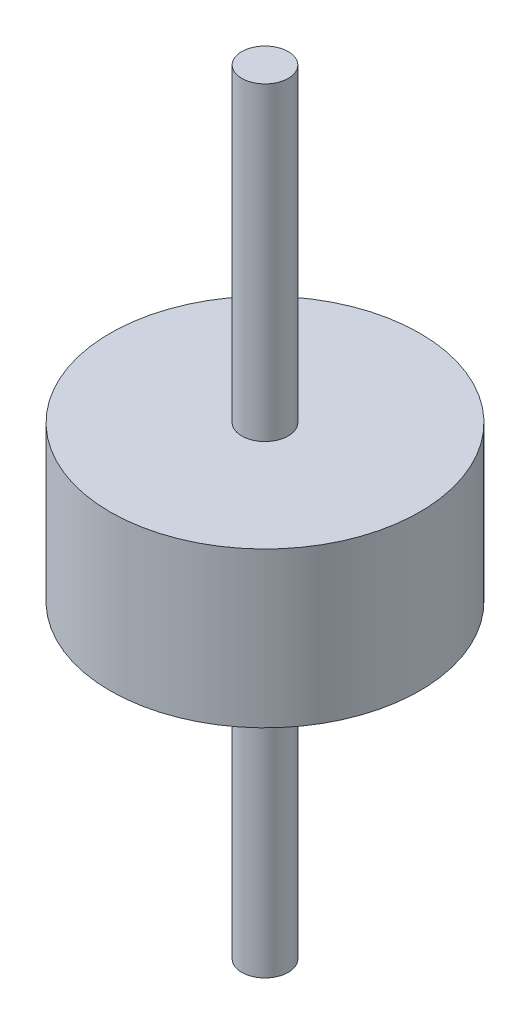
SolidWorks part; units mm, degrees
ref_plane "Front Plane" through (0, 0, 0) normal (0, 0, 1) x (1, 0, 0)
ref_plane "Top Plane" through (0, 0, 0) normal (0, 1, 0) x (1, 0, 0)
ref_plane "Right Plane" through (0, 0, 0) normal (1, 0, 0) x (0, 0, -1)
sketch "Sketch1" plane through (0, 0, 0) normal (0, 1, 0) x (1, 0, 0)
  circle A0 centre (-10.1199, -11.3021) radius 5.08
  dimension "D1" = 10.16
extrude "Boss-Extrude2" add sketch "Sketch1" along normal blind 5.08
sketch "Sketch2" plane through (0, 5.08, 0) normal (0, 1, 0) x (1, 0, 0)
  circle A0 centre (-10.1199, -11.3021) radius 0.762
  dimension "D1" = 1.524
extrude "Boss-Extrude3" add sketch "Sketch2" along normal blind 10.16 contours A0
sketch "Sketch3" plane through (0, 0, 0) normal (0, -1, 0) x (1, 0, 0)
  circle A1 centre (-10.1199, 11.3021) radius 0.762
  dimension "D1" = 1.524
extrude "Boss-Extrude4" add sketch "Sketch3" along normal blind 10.16
